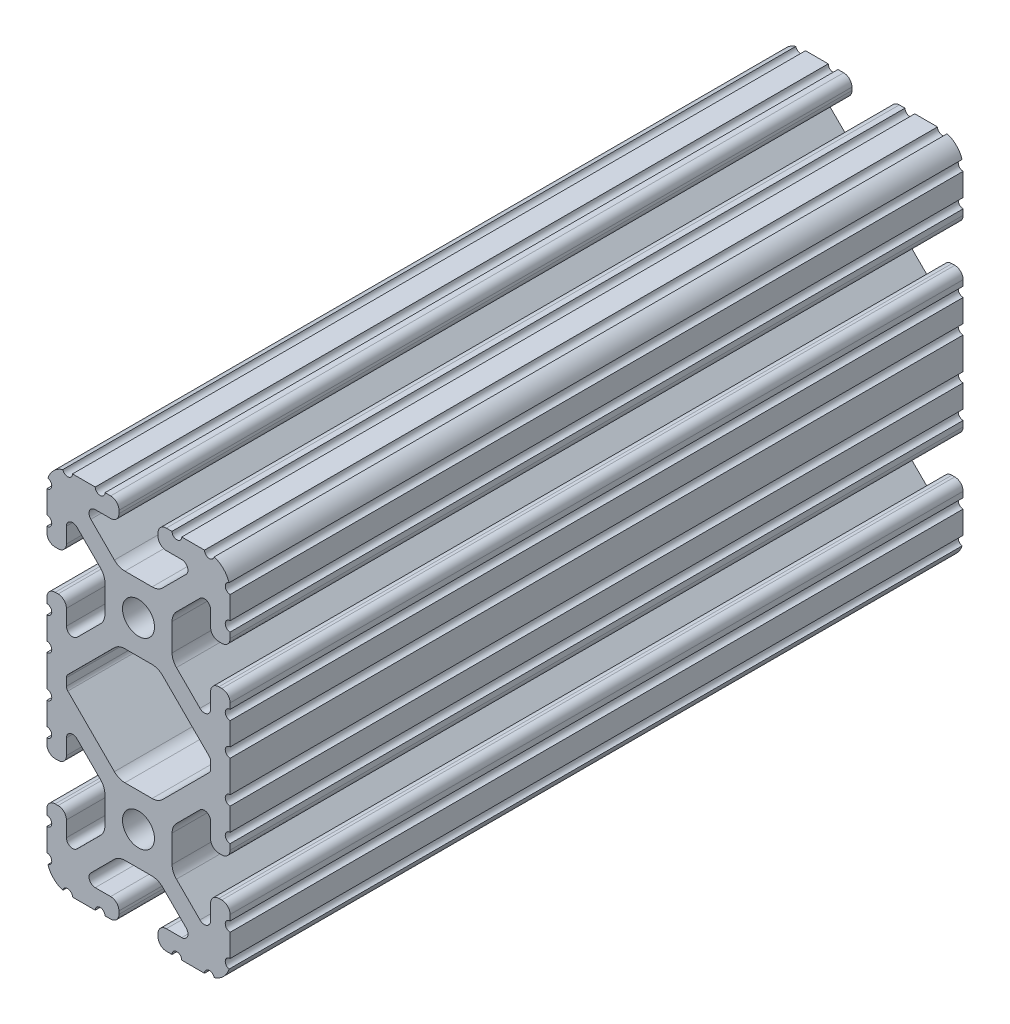
SolidWorks part; units mm, degrees
ref_plane "Front Plane" through (0, 0, 0) normal (0, 0, 1) x (1, 0, 0)
ref_plane "Top Plane" through (0, 0, 0) normal (0, 1, 0) x (1, 0, 0)
ref_plane "Right Plane" through (0, 0, 0) normal (1, 0, 0) x (0, 0, -1)
sketch "Sketch2" plane through (0, 0, 0) normal (0, 0, 1) x (1, 0, 0)
  line L0 (0, 38.1) -> (0, -38.1) construction
  line L1 (-19.05, 0) -> (19.05, 0) construction
  line L2 (4.064, -38.1) -> (19.05, -38.1)
  line L3 (19.05, -38.1) -> (19.05, -23.114)
  line L4 (4.064, -38.1) -> (4.064, -34.036)
  line L5 (4.064, -34.036) -> (12.1123, -34.036)
  line L6 (12.1123, -34.036) -> (4.1113, -26.035)
  line L7 (0, -19.05) -> (19.05, -38.1) construction
  line L8 (19.05, -23.114) -> (14.986, -23.114)
  line L9 (14.986, -23.114) -> (14.986, -31.1623)
  line L10 (14.986, -31.1623) -> (6.985, -23.1613)
  circle A0 centre (0, -19.05) radius 3.3274
  arc A1 (8.9963, -34.036) -> (9.909, -31.8326) centre (8.9963, -32.7453) ccw construction
  point P8 (0, -26.035)
  dimension "Center Hole Diameter" = 6.6548
  dimension "Rail Height" = 76.2
  dimension "Rail Width" = 38.1
  dimension "T-Slot Width" = 8.128
  dimension "Slot Inner Width" = 20.574
  dimension "Thickness" = 4.064
  dimension "Slot Depth" = 8.001
  dimension "D1" = 4.064
  dimension "C to C" = 38.1
sketch "Sketch3" plane through (0, 0, 0) normal (1, 0, 0) x (0, 0, -1)
  line L0 (-76.2, -38.1) -> (76.2, -38.1) construction
  line L1 (-50.8, 0) -> (50.8, 0) construction
  dimension "Length" = 152.4
  dimension "D1" = 25.4
sketch "Sketch4" plane through (0, 0, 0) normal (0, 0, 1) x (1, 0, 0)
  line L0 (5.7912, -38.1) -> (14.3002, -38.1)
  line L1 (4.064, -38.1) -> (19.05, -38.1) construction
  line L2 (4.064, -38.1) -> (4.064, -34.036) construction
  line L3 (4.064, -34.036) -> (12.1123, -34.036) construction
  line L4 (4.064, -35.7632) -> (4.064, -36.3728)
  line L5 (5.7912, -34.036) -> (8.9963, -34.036)
  line L6 (0, -26.035) -> (2.833, -26.035)
  line L7 (12.1123, -34.036) -> (4.1113, -26.035) construction
  line L8 (5.0152, -26.9389) -> (9.909, -31.8326)
  line L9 (19.05, -38.1) -> (19.05, -23.114) construction
  line L10 (14.986, -31.1623) -> (6.985, -23.1613) construction
  line L11 (14.986, -23.114) -> (14.986, -31.1623) construction
  line L12 (14.986, -28.0463) -> (14.986, -24.8412)
  line L13 (19.05, -23.114) -> (14.986, -23.114) construction
  line L14 (16.7132, -23.114) -> (17.3228, -23.114)
  line L15 (19.05, -24.8412) -> (19.05, -33.3502)
  line L16 (12.7826, -28.959) -> (7.8889, -24.0652)
  line L17 (6.985, -19.05) -> (6.985, -21.883)
  line L19 (0, -26.035) -> (0, -22.3774)
  line L20 (0, 38.1) -> (0, -38.1) construction
  line L21 (6.985, -19.05) -> (3.3274, -19.05)
  arc A0 (4.064, -36.3728) -> (5.7912, -38.1) centre (5.7912, -36.3728) ccw
  circle A1 centre (0, -19.05) radius 3.3274 construction
  arc A2 (4.064, -35.7632) -> (5.7912, -34.036) centre (5.7912, -35.7632) cw
  arc A3 (8.9963, -34.036) -> (9.909, -31.8326) centre (8.9963, -32.7453) ccw
  arc A4 (2.833, -26.035) -> (5.0152, -26.9389) centre (2.833, -29.1211) cw
  arc A5 (14.3002, -38.1) -> (19.05, -33.3502) centre (14.3002, -33.3502) ccw
  arc A6 (12.7826, -28.959) -> (14.986, -28.0463) centre (13.6953, -28.0463) ccw
  arc A7 (14.986, -24.8412) -> (16.7132, -23.114) centre (16.7132, -24.8412) cw
  arc A8 (17.3228, -23.114) -> (19.05, -24.8412) centre (17.3228, -24.8412) cw
  arc A9 (7.8889, -24.0652) -> (6.985, -21.883) centre (10.0711, -21.883) cw
  arc A11 (0, -22.3774) -> (3.3274, -19.05) centre (0, -19.05) ccw
  dimension "D1" = 4.7498
  dimension "D2" = 3.0861
  dimension "D3" = 1.7272
extrude "Boss-Extrude1" add sketch "Sketch4" along normal mid plane 152.4
sketch "Sketch5" plane through (0, 0, 0) normal (0, 0, 1) x (1, 0, 0)
  line L0 (4.064, -38.1) -> (19.05, -38.1) construction
  line L1 (5.7912, -34.036) -> (8.9963, -34.036) construction
  line L3 (0, -19.05) -> (19.05, -38.1) construction
  line L4 (8.9963, -34.036) -> (8.9963, -38.1) construction
  line L5 (12.1123, -34.036) -> (4.1113, -26.035) construction
  circle A0 centre (14.7395, -38.1) radius 1.016
  circle A1 centre (7.9803, -38.1) radius 1.016
  circle A2 centre (19.05, -33.7895) radius 1.016
  circle A3 centre (19.05, -27.0303) radius 1.016
  point P10 (7.3938, -34.036)
  point P12 (13.6953, -28.0463)
  dimension "D1" = 2.032
extrude "Cut-Extrude1" cut sketch "Sketch5" against normal through all both and the other way through all
mirror "Mirror1" about plane through (6.985, -19.05, 76.2) normal (0, -1, 0) of bodies 137 134
sketch "Sketch6" plane through (0, 0, 0) normal (0, 0, 1) x (1, 0, 0)
  line L0 (19.05, -3.2945) -> (19.05, 0)
  line L1 (19.05, 0) -> (13.7235, 0)
  line L2 (-19.05, 0) -> (19.05, 0) construction
  line L3 (13.7235, 0) -> (13.7235, -4.3105)
  line L4 (13.7235, -4.3105) -> (18.034, -4.3105)
  circle A0 centre (19.05, -4.3105) radius 1.016 construction
  arc A1 (19.05, -3.2945) -> (18.034, -4.3105) centre (19.05, -4.3105) ccw
  arc A4 (18.8293, -3.3188) -> (19.05, -5.3265) centre (19.05, -4.3105) ccw construction
  arc A6 (13.7235, 0) -> (15.7312, -0.2207) centre (14.7395, 0) ccw construction
extrude "Boss-Extrude2" add sketch "Sketch6" along normal mid plane 152.4
sketch "Sketch7" plane through (0, 0, 0) normal (0, 0, 1) x (1, 0, 0)
  line L0 (7.4621, -8.7142) -> (14.6884, -1.4879)
  line L1 (5.0152, -11.1611) -> (9.909, -6.2674) construction
  line L2 (14.986, -0.7695) -> (14.986, 0)
  line L3 (0, 0) -> (14.986, 0)
  line L4 (-19.05, 0) -> (19.05, 0) construction
  line L5 (0, 0) -> (7.4621, -8.7142)
  arc A0 (14.6884, -1.4879) -> (14.986, -0.7695) centre (13.97, -0.7695) ccw
  arc A3 (19.05, -3.2945) -> (19.05, -5.3265) centre (19.05, -4.3105) ccw construction
extrude "Cut-Extrude2" cut sketch "Sketch7" against normal through all both and the other way through all
mirror "Mirror2" about plane through (0, 0, 0) normal (0, 1, 0) of bodies 139 135
mirror "Mirror3" about plane through (0, 0, 0) normal (1, 0, 0) of bodies 136
equation "\"D1@Boss-Extrude1\"=\"Length@Sketch3\""
equation "\"D1@Sketch2\"=\"Thickness@Sketch2\""
equation "\"D2@Sketch4\"=\"Slot Inner Width@Sketch2\"*0.15"
equation "\"D1@Sketch4\"=\"D3@Sketch4\"*2.75"
equation "\"D3@Sketch4\"=\"Thickness@Sketch2\"*0.425"
equation "\"D1@Sketch5\"=\"Thickness@Sketch2\"*0.5"
equation "\"D1@Boss-Extrude2\"=\"Length@Sketch3\""
